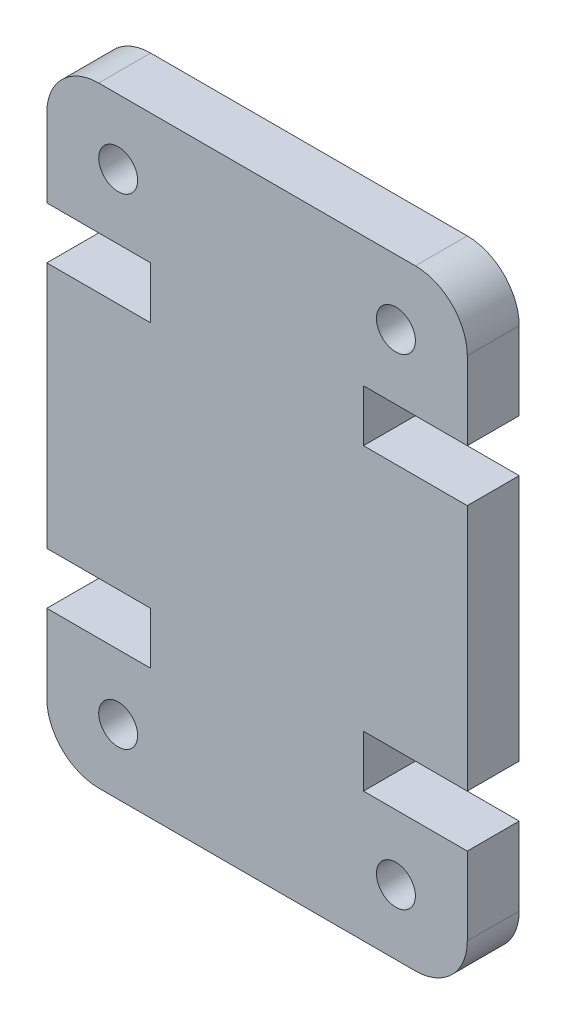
SolidWorks part; units mm, degrees
ref_plane "Front Plane" through (0, 0, 0) normal (0, 0, 1) x (1, 0, 0)
ref_plane "Top Plane" through (0, 0, 0) normal (0, 1, 0) x (1, 0, 0)
ref_plane "Right Plane" through (0, 0, 0) normal (1, 0, 0) x (0, 0, -1)
sketch "Sketch1" plane through (0, 0, 0) normal (0, 0, 1) x (1, 0, 0)
  line L0 (8.1, 23.525) -> (8.1, 0) construction
  line L1 (0, 11.7625) -> (16.2, 11.7625) construction
  line L2 (16.2, 5) -> (16.2, 2)
  line L3 (12.2, 5) -> (16.2, 5)
  line L4 (16.2, 7) -> (12.2, 7)
  line L5 (12.2, 7) -> (12.2, 5)
  line L6 (16.2, 7) -> (16.2, 16.525)
  line L7 (0, 18.525) -> (0, 21.525)
  line L8 (4, 18.525) -> (0, 18.525)
  line L9 (0, 16.525) -> (4, 16.525)
  line L10 (4, 16.525) -> (4, 18.525)
  line L11 (2, 23.525) -> (14.2, 23.525)
  line L12 (12.2, 16.525) -> (12.2, 18.525)
  line L13 (16.2, 16.525) -> (12.2, 16.525)
  line L14 (12.2, 18.525) -> (16.2, 18.525)
  line L15 (16.2, 18.525) -> (16.2, 21.525)
  line L20 (0, 7) -> (0, 16.525)
  line L23 (2, 0) -> (14.2, 0)
  line L30 (4, 7) -> (4, 5)
  line L32 (0, 7) -> (4, 7)
  line L33 (4, 5) -> (0, 5)
  line L39 (0, 5) -> (0, 2)
  circle A0 centre (13.45, 2.5) radius 0.75
  arc A2 (16.2, 2) -> (14.2, 0) centre (14.2, 2) cw
  circle A4 centre (2.75, 21.025) radius 0.75
  arc A5 (0, 21.525) -> (2, 23.525) centre (2, 21.525) cw
  arc A7 (16.2, 21.525) -> (14.2, 23.525) centre (14.2, 21.525) ccw
  circle A9 centre (13.45, 21.025) radius 0.75
  arc A11 (0, 2) -> (2, 0) centre (2, 2) ccw
  circle A13 centre (2.75, 2.5) radius 0.75
  point P18 (8.1, 11.7625)
  dimension "D2" = 2
  dimension "D4" = 1.5
  dimension "D3" = 2.75
  dimension "D5" = 8.1
  dimension "D6" = 2.5
  dimension "D7" = 5
  dimension "D10" = 11.7625
extrude "Boss-Extrude1" add sketch "Sketch1" along normal blind 2
equation "\"D10@Sketch1\"= ( \"HL@parametersSketch@prostheticParameters.SLDPRT\" * 0.165 - 3 - 4 ) / 2 'MIP length - Sil. Sht MIP - Sil. Sht DIP"
equation "\"D5@Sketch1\"= \"fingerWidth@parametersSketch@prostheticParameters.SLDPRT\" / 2'MIP width"
